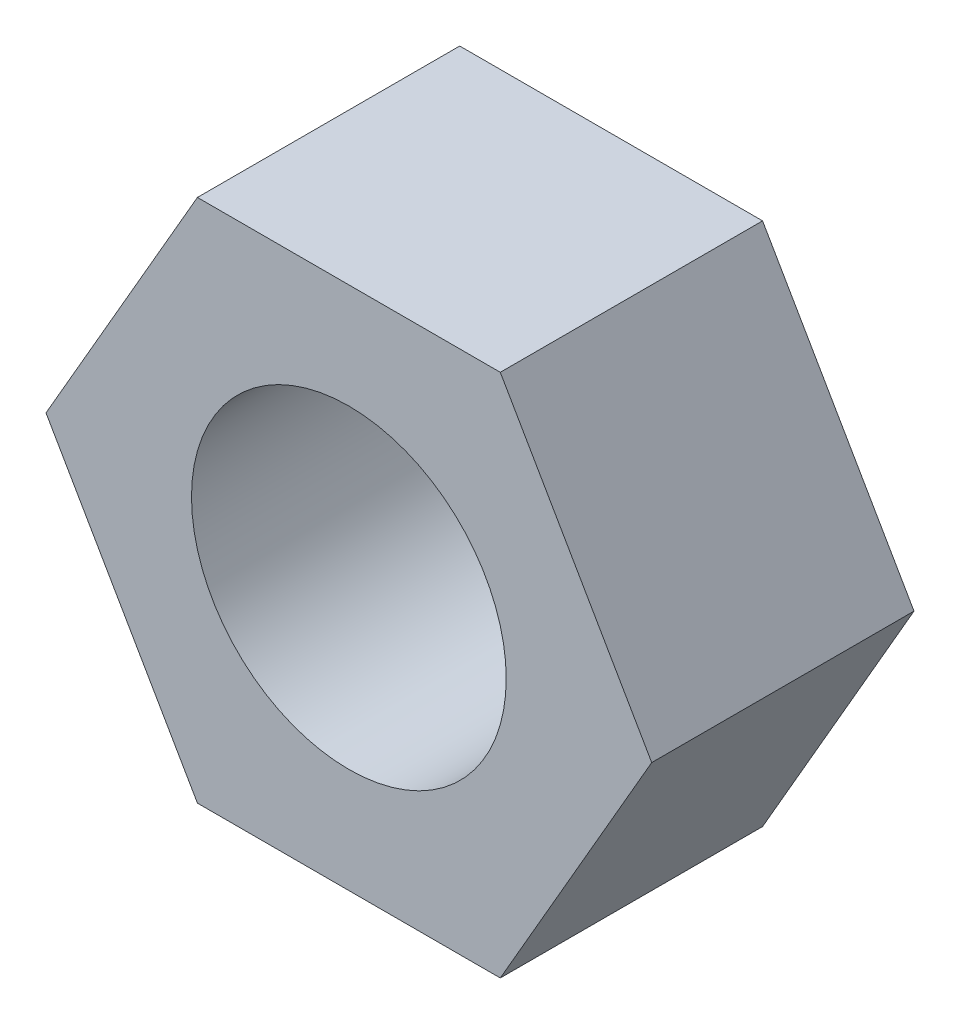
SolidWorks part; units mm, degrees
ref_plane "Plano frontal" through (0, 0, 0) normal (0, 0, 1) x (1, 0, 0)
ref_plane "Plano superior" through (0, 0, 0) normal (0, 1, 0) x (1, 0, 0)
ref_plane "Plano direito" through (0, 0, 0) normal (1, 0, 0) x (0, 0, -1)
sketch "Esboço1" plane through (0, 0, 0) normal (0, 0, 1) x (1, 0, 0)
  line L0 (-2.8868, 5) -> (2.8868, 5)
  line L1 (2.8868, 5) -> (5.7735, 0)
  line L2 (5.7735, 0) -> (2.8868, -5)
  line L3 (2.8868, -5) -> (-2.8868, -5)
  line L4 (-2.8868, -5) -> (-5.7735, 0)
  line L5 (-5.7735, 0) -> (-2.8868, 5)
  line L6 (-2.8868, 5) -> (-2.8868, -5) construction
  line L7 (2.8868, 5) -> (2.8868, -5) construction
  line L8 (-5.7735, 0) -> (2.8868, -5) construction
  line L9 (-5.7735, 0) -> (5.7735, 0) construction
  circle A0 centre (0, 0) radius 3
  point P6 (0, 0)
  dimension "D2" = 6
  dimension "D1" = 10
extrude "Ressalto-extrusão1" add sketch "Esboço1" along normal blind 5
